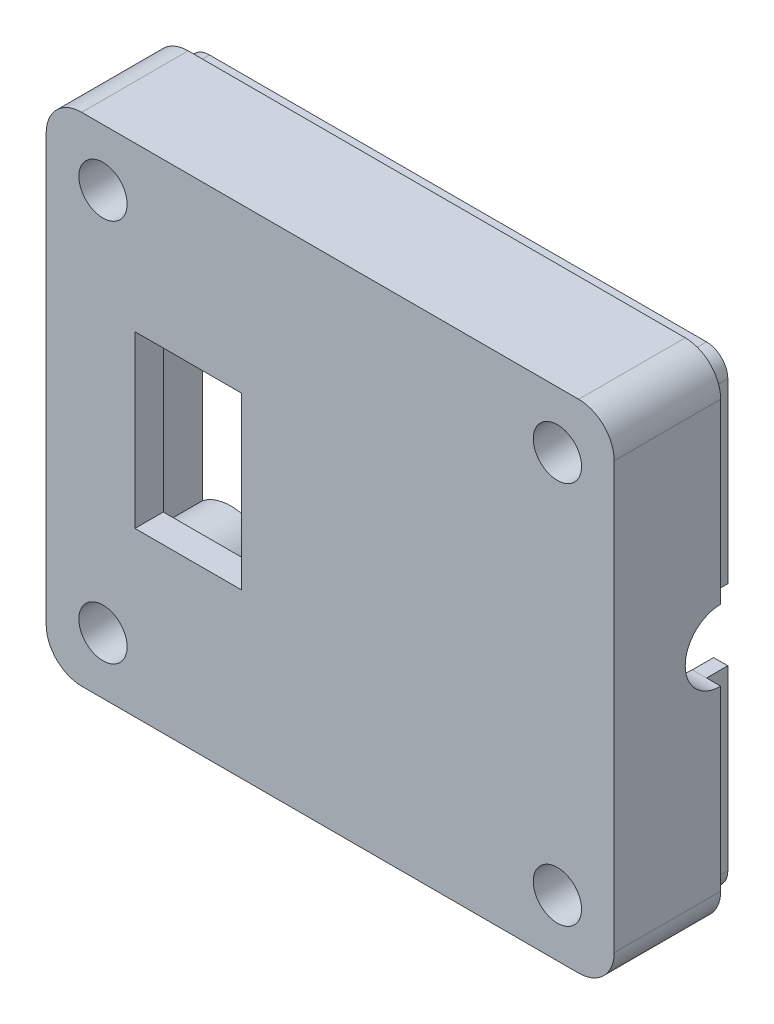
SolidWorks part; units mm, degrees
ref_plane "Face" through (0, 0, 0) normal (0, 0, 1) x (1, 0, 0)
ref_plane "Dessus" through (0, 0, 0) normal (0, 1, 0) x (1, 0, 0)
ref_plane "Droite" through (0, 0, 0) normal (1, 0, 0) x (0, 0, -1)
sketch "Esquisse1" plane through (0, 0, 0) normal (0, 0, 1) x (1, 0, 0)
  line L2 (-3.1227, -42.358) -> (-3.1227, -7.358)
  line L3 (-3.1227, -7.358) -> (36.8773, -7.358)
  line L4 (36.8773, -42.358) -> (36.8773, -7.358)
  line L6 (34.8773, -9.358) -> (34.8773, -40.358)
  line L8 (-1.1227, -9.358) -> (-1.1227, -40.358)
  line L18 (-3.1227, -42.358) -> (36.8773, -42.358)
  line L29 (34.8773, -40.358) -> (-1.1227, -40.358)
  line L32 (-1.1227, -9.358) -> (34.8773, -9.358)
  line L33 (-3.1227, -7.358) -> (-3.1227, -42.358) construction
  dimension "D1" = 2
  dimension "D2" = 40
  dimension "D3" = 36
  dimension "D4" = 2
  dimension "D5" = 2
  dimension "D6" = 35
extrude "Boss.-Extru.1" add sketch "Esquisse1" along normal blind 5.5
sketch "Esquisse2" plane through (0, 0, 5.5) normal (0, 0, 1) x (1, 0, 0)
  line L1 (-3.1227, -7.358) -> (36.8773, -7.358)
  line L2 (-3.1227, -7.358) -> (-3.1227, -42.358)
  line L3 (-3.1227, -42.358) -> (36.8773, -42.358)
  line L4 (36.8773, -7.358) -> (36.8773, -42.358)
extrude "Boss.-Extru.2" add sketch "Esquisse2" along normal blind 2
sketch "Esquisse3" plane through (36.8773, 0, 0) normal (1, 0, 0) x (0, 0, -1)
  line L0 (0, -42.358) -> (0, -7.358) construction
  line L1 (0, -22.358) -> (0, -27.358)
  arc A0 (0, -22.358) -> (0, -27.358) centre (0, -24.858) ccw
  dimension "D1" = 2.5
extrude "Enlèv. mat.-Extru.1" cut sketch "Esquisse3" against normal up to next
sketch "Esquisse4" plane through (0, 0, 5.5) normal (0, 0, -1) x (-1, 0, 0)
  line L0 (-32.8773, -24.858) -> (-16.8773, -24.858) construction
  line L1 (-16.8773, -24.858) -> (-0.8773, -24.858) construction
  line L2 (-32.8773, -11.358) -> (-32.8773, -38.358) construction
  line L3 (-32.8773, -24.858) -> (-33.75, -24.858) construction
  line L12 (-16.8773, -38.358) -> (-16.8773, -40.358) construction
  line L13 (-0.8773, -11.358) -> (-0.8773, -38.358) construction
  line L14 (-0.8773, -38.358) -> (-32.8773, -38.358) construction
  line L15 (-16.8773, -9.358) -> (-16.8773, -40.358) construction
  line L16 (-30.3155, -9.358) -> (-34.8773, -9.358)
  line L17 (-16.8773, -40.358) -> (-16.8773, -38.358) construction
  line L18 (-17.8773, -32.858) -> (-17.8773, -40.358)
  line L19 (-17.8773, -40.358) -> (-15.8773, -40.358)
  line L20 (-15.8773, -31.858) -> (-15.8773, -40.358)
  line L24 (1.1227, -9.358) -> (-34.8773, -9.358) construction
  line L36 (-16.8773, -9.358) -> (-16.8773, -11.358) construction
  line L37 (-16.8773, -11.358) -> (-16.8773, -9.358) construction
  line L38 (-34.8773, -13.9198) -> (-34.8773, -9.358)
  line L40 (-34.8773, -40.358) -> (-34.8773, -35.7963)
  line L41 (-34.8773, -40.358) -> (-30.3155, -40.358)
  line L44 (-34.8773, -16.858) -> (-17.8773, -16.858)
  line L45 (1.1227, -40.358) -> (1.1227, -35.7963)
  line L46 (1.1227, -13.9198) -> (1.1227, -35.7963) construction
  line L47 (-3.439, -40.358) -> (1.1227, -40.358)
  line L48 (-34.8773, -18.858) -> (-34.8773, -16.858)
  line L49 (-32.8773, -11.358) -> (-0.8773, -11.358) construction
  line L50 (-34.8773, -30.858) -> (-16.8773, -30.858)
  line L51 (-34.8773, -18.858) -> (-16.8773, -18.858)
  line L52 (-15.8773, -17.858) -> (-15.8773, -9.358)
  line L53 (-34.8773, -30.858) -> (-34.8773, -32.858)
  line L54 (-17.8773, -9.358) -> (-15.8773, -9.358)
  line L57 (-34.8773, -32.858) -> (-17.8773, -32.858)
  line L59 (-32.8773, -38.358) -> (-32.8773, -42.358) construction
  line L60 (3.1227, -42.358) -> (-36.8773, -42.358) construction
  line L61 (-17.8773, -16.858) -> (-17.8773, -9.358)
  line L62 (-32.8773, -38.358) -> (-36.8773, -38.358) construction
  line L64 (-36.8773, -42.358) -> (-36.8773, -27.358) construction
  line L66 (1.1227, -9.358) -> (1.1227, -13.9198)
  line L67 (-34.8773, -40.358) -> (1.1227, -40.358) construction
  line L68 (-3.439, -9.358) -> (1.1227, -9.358)
  line L69 (1.1227, -35.7963) -> (1.1227, -40.358)
  line L70 (1.1227, -9.358) -> (1.1227, -40.358) construction
  arc A6 (-34.8773, -13.9198) -> (-30.3155, -9.358) centre (-32.8773, -11.358) ccw
  arc A7 (-30.3155, -40.358) -> (-34.8773, -35.7963) centre (-32.8773, -38.358) ccw
  arc A8 (-3.439, -9.358) -> (1.1227, -13.9198) centre (-0.8773, -11.358) ccw
  arc A9 (1.1227, -35.7963) -> (-3.439, -40.358) centre (-0.8773, -38.358) ccw
  arc A13 (-16.8773, -30.858) -> (-15.8773, -31.858) centre (-16.8773, -31.858) cw
  arc A14 (-16.8773, -18.858) -> (-15.8773, -17.858) centre (-16.8773, -17.858) ccw
  dimension "D2" = 2
  dimension "D5" = 6
  dimension "D6" = 18
  dimension "D3" = 1
  dimension "D7" = 3.25
  dimension "D4" = 1
  dimension "D8" = 4
  dimension "D1" = 2
extrude "Boss.-Extru.3" add sketch "Esquisse4" along normal blind 7
sketch "Esquisse9" plane through (6.5, 0, 7.5) normal (0, 0, -1) x (-1, 0, 0)
  line L0 (-28.3773, -30.358) -> (-28.3773, -19.358) construction
  line L7 (-4.1273, -18.858) -> (3.3727, -18.858)
  line L8 (-4.1273, -18.858) -> (-4.1273, -30.858)
  line L9 (-4.1273, -30.858) -> (3.3727, -30.858)
  line L10 (3.3727, -18.858) -> (3.3727, -30.858)
  line L12 (-4.1273, -24.858) -> (3.3727, -24.858) construction
  dimension "D3" = 7.5
  dimension "D1" = 24.25
  dimension "D2" = 12
extrude "Enlèv. mat.-Extru.2" cut sketch "Esquisse9" along normal up to next contours L7 L10 L9 L8
hole_wizard "Dégagement M31" positions "Esquisse10" profile "Esquisse11" hole size "M3" standard "ISO" end condition through all
sketch "Esquisse10" plane through (0, 0, 7.5) normal (0, 0, 1) x (1, 0, 0)
  point P0 (0.8773, -11.358)
  point P2 (32.8773, -38.358)
  point P10 (32.8773, -11.358)
  point P13 (0.8773, -38.358)
sketch "Esquisse11" plane through (0.8773, -11.358, 7.5) normal (1, 0, 0) x (0, -1, 0)
  line L0 (0, 0) -> (0, 9)
  line L1 (0, 9) -> (1.7, 9)
  line L2 (1.7, 9) -> (1.7, 0)
  line L5 (1.7, 0) -> (0, 0)
  line L11 (0, -6.35) -> (0, 107.95) construction
  dimension "Diamètre du perçage jusqu'au prochain" = 3.4
  dimension "Profondeur du perçage jusqu'au prochain" = 9
fillet "Congé1" radius 2.5 4 edges at (-3.1227, -42.358, 3.75) (-3.1227, -7.358, 3.75) (36.8773, -7.358, 3.75) (36.8773, -42.358, 3.75)
sketch "Esquisse13" plane through (0, 0, 0) normal (0, 0, -1) x (-1, 0, 0)
  line L0 (-35.8773, -27.358) -> (-34.8773, -27.358)
  line L1 (-35.8773, -22.358) -> (-34.8773, -22.358)
  line L3 (-34.8773, -22.358) -> (-36.8773, -22.358) construction
  line L5 (1.1227, -13.9198) -> (1.1227, -35.7963) construction
  line L6 (0.6227, -7.358) -> (-34.3773, -7.358) construction
  line L7 (3.1227, -39.858) -> (3.1227, -9.858) construction
  line L8 (0.6227, -42.358) -> (-34.3773, -42.358) construction
  line L9 (-36.8773, -39.858) -> (-36.8773, -27.358) construction
  line L10 (-36.8773, -22.358) -> (-36.8773, -9.858) construction
  line L39 (-34.8773, -27.358) -> (-34.8773, -39.858)
  line L40 (-34.3773, -40.358) -> (0.6227, -40.358)
  line L41 (1.1227, -39.858) -> (1.1227, -9.8618)
  line L42 (0.619, -9.358) -> (-34.3773, -9.358)
  line L43 (-34.8773, -9.858) -> (-34.8773, -22.358)
  line L51 (-35.8773, -9.858) -> (-35.8773, -22.358)
  line L52 (0.6227, -8.358) -> (-34.3773, -8.358)
  line L53 (2.1227, -39.858) -> (2.1227, -9.858)
  line L54 (-34.3773, -41.358) -> (0.6227, -41.358)
  line L55 (-35.8773, -27.358) -> (-35.8773, -39.858)
  arc A0 (-36.8773, -39.858) -> (-34.3773, -42.358) centre (-34.3773, -39.858) ccw construction
  arc A1 (0.6227, -42.358) -> (3.1227, -39.858) centre (0.6227, -39.858) ccw construction
  arc A2 (3.1227, -9.858) -> (0.6227, -7.358) centre (0.6227, -9.858) ccw construction
  arc A3 (-34.3773, -7.358) -> (-36.8773, -9.858) centre (-34.3773, -9.858) ccw construction
  arc A20 (-34.8773, -39.858) -> (-34.3773, -40.358) centre (-34.3773, -39.858) ccw
  arc A21 (0.6227, -40.358) -> (1.1227, -39.858) centre (0.6227, -39.858) ccw
  arc A22 (1.1227, -9.8618) -> (0.619, -9.358) centre (0.619, -9.8618) ccw
  arc A23 (-34.3773, -9.358) -> (-34.8773, -9.858) centre (-34.3773, -9.858) ccw
  arc A28 (-34.3773, -8.358) -> (-35.8773, -9.858) centre (-34.3773, -9.858) ccw
  arc A29 (2.1227, -9.858) -> (0.6227, -8.358) centre (0.6227, -9.858) ccw
  arc A30 (0.6227, -41.358) -> (2.1227, -39.858) centre (0.6227, -39.858) ccw
  arc A31 (-35.8773, -39.858) -> (-34.3773, -41.358) centre (-34.3773, -39.858) ccw
  dimension "D3" = 1
  dimension "D7" = 0.5
  dimension "D9" = 0.5
  dimension "D10" = 0.5038
  dimension "D11" = 0.5
  dimension "D6" = 1
  dimension "D8" = 1
  dimension "D12" = 1
  dimension "D13" = 1
  dimension "D2" = 1
  dimension "D4" = 1
  dimension "D5" = 1
  dimension "D14" = 1
  dimension "D15" = 1
  dimension "D16" = 1
  dimension "D17" = 1
  dimension "D18" = 1
  dimension "D19" = 5
extrude "Boss.-Extru.6" add sketch "Esquisse13" along normal blind 1.5
